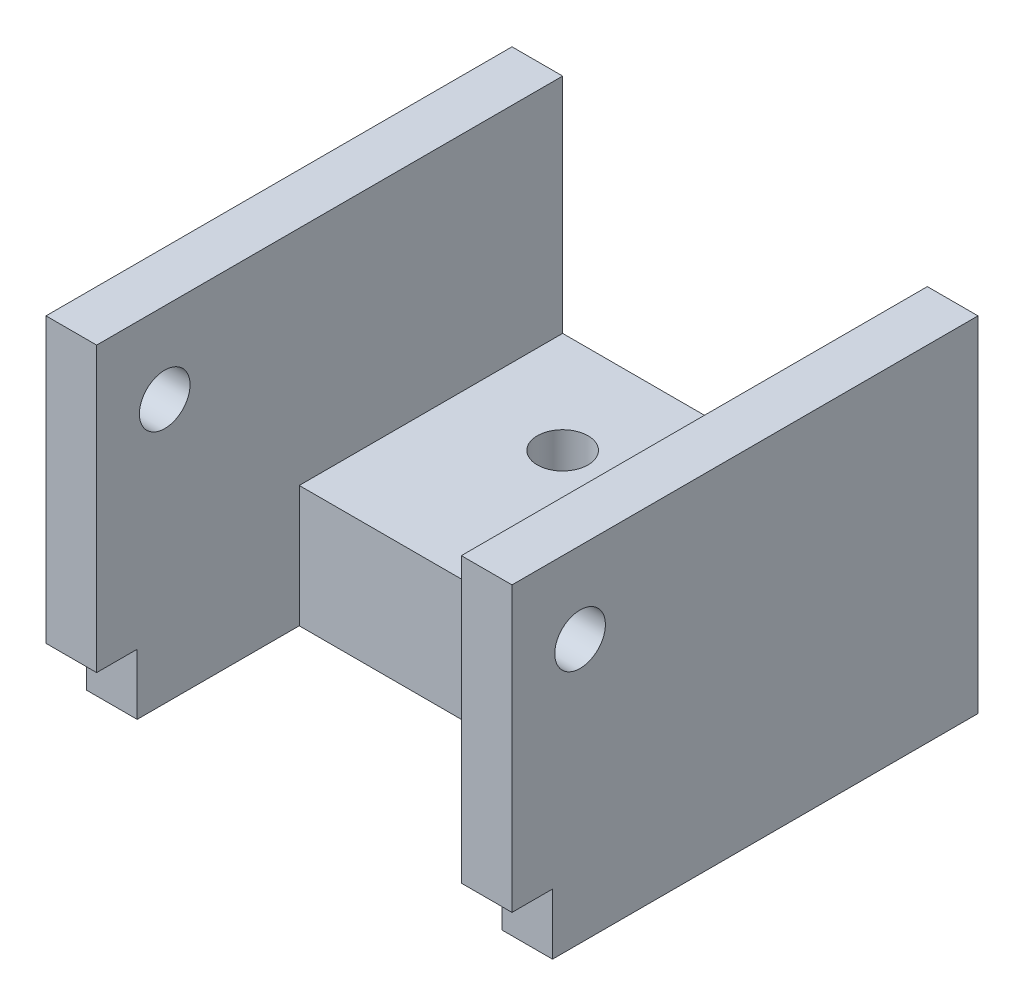
SolidWorks part; units mm, degrees
ref_plane "Front Plane" through (0, 0, 0) normal (0, 0, 1) x (1, 0, 0)
ref_plane "Top Plane" through (0, 0, 0) normal (0, 1, 0) x (1, 0, 0)
ref_plane "Right Plane" through (0, 0, 0) normal (1, 0, 0) x (0, 0, -1)
sketch "Sketch1" plane through (0, 0, 0) normal (1, 0, 0) x (0, 0, -1)
  line L1 (-50.9711, 32.347) -> (-27.9711, 32.347)
  line L2 (-50.9711, 32.347) -> (-50.9711, 15.347)
  line L3 (-50.9711, 15.347) -> (-27.9711, 15.347)
  line L4 (-27.9711, 32.347) -> (-27.9711, 15.347)
  dimension "D1" = 23
  dimension "D2" = 17
extrude "Boss-Extrude1" add sketch "Sketch1" along normal blind 2.5
sketch "Sketch2" plane through (2.5, 0, 0) normal (1, 0, 0) x (0, 0, -1)
  line L1 (-27.9711, 15.347) -> (-40.9711, 15.347)
  line L2 (-27.9711, 15.347) -> (-27.9711, 21.347)
  line L3 (-27.9711, 21.347) -> (-40.9711, 21.347)
  line L4 (-40.9711, 15.347) -> (-40.9711, 21.347)
  dimension "D1" = 6
  dimension "D2" = 13
extrude "Boss-Extrude2" add sketch "Sketch2" along normal blind 18
sketch "Sketch3" plane through (20.5, 0, 0) normal (1, 0, 0) x (0, 0, -1)
  line L1 (-27.9711, 15.347) -> (-50.9711, 15.347)
  line L2 (-27.9711, 15.347) -> (-27.9711, 32.347)
  line L3 (-27.9711, 32.347) -> (-50.9711, 32.347)
  line L4 (-50.9711, 15.347) -> (-50.9711, 32.347)
extrude "Boss-Extrude3" add sketch "Sketch3" along normal blind 2.5
sketch "Sketch4" plane through (23, 0, 0) normal (1, 0, 0) x (0, 0, -1)
  line L0 (-27.9711, 32.347) -> (-50.9711, 32.347) construction
  line L1 (-27.9711, 15.347) -> (-27.9711, 32.347) construction
  circle A0 centre (-47.6111, 28.347) radius 1.25
  dimension "D1" = 4
  dimension "D2" = 19.64
sketch "Sketch5" plane through (23, 0, 0) normal (1, 0, 0) x (0, 0, -1)
  line L1 (-50.9711, 15.347) -> (-48.9711, 15.347)
  line L2 (-50.9711, 15.347) -> (-50.9711, 18.347)
  line L3 (-50.9711, 18.347) -> (-48.9711, 18.347)
  line L4 (-48.9711, 15.347) -> (-48.9711, 18.347)
  dimension "D1" = 3
  dimension "D2" = 2
extrude "Cut-Extrude1" cut sketch "Sketch5" against normal through all
sketch "Sketch6" plane through (0, 21.347, 0) normal (0, 1, 0) x (1, 0, 0)
  line L0 (20.5, -27.9711) -> (2.5, -27.9711) construction
  line L1 (2.5, -27.9711) -> (2.5, -40.9711) construction
  circle A0 centre (11.5, -32.9711) radius 1.8
  dimension "D1" = 5
  dimension "D2" = 9
extrude "Cut-Extrude2" [suppressed] cut sketch "Sketch6" against normal through all
extrude "Cut-Extrude3" cut sketch "Sketch4" against normal through all
sketch "Sketch7" plane through (0, 21.347, 0) normal (0, 1, 0) x (1, 0, 0)
  line L0 (2.5, -27.9711) -> (2.5, -40.9711) construction
  line L1 (20.5, -27.9711) -> (20.5, -40.9711) construction
  circle A0 centre (7.5, -32.9711) radius 1.25
  circle A1 centre (15.5, -32.9711) radius 1.25
  dimension "D1" = 2.5
  dimension "D2" = 5
  dimension "D3" = 5
extrude "Cut-Extrude4" cut sketch "Sketch7" against normal blind 10
